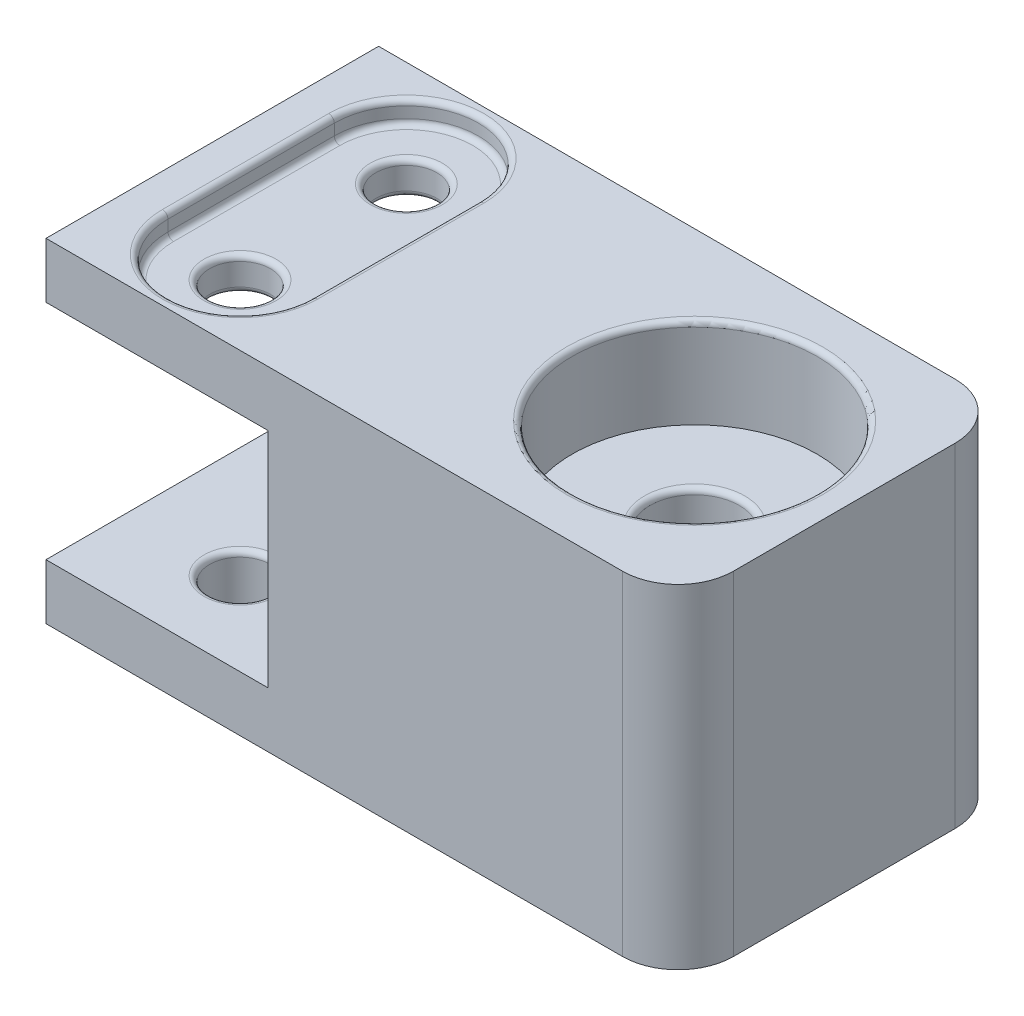
SolidWorks part; units mm, degrees
ref_plane "Front Plane" through (0, 0, 0) normal (0, 0, 1) x (1, 0, 0)
ref_plane "Top Plane" through (0, 0, 0) normal (0, 1, 0) x (1, 0, 0)
ref_plane "Right Plane" through (0, 0, 0) normal (1, 0, 0) x (0, 0, -1)
sketch "Sketch4" plane through (0, 0, 0) normal (0, 1, 0) x (1, 0, 0)
  line L1 (-28.5, -15) -> (28.5, -15)
  line L2 (-28.5, -15) -> (-28.5, 15)
  line L3 (-28.5, 15) -> (28.5, 15)
  line L4 (28.5, -15) -> (28.5, 15)
  line L5 (-28.5, -15) -> (28.5, 15) construction
  line L6 (-28.5, 15) -> (28.5, -15) construction
  point P0 (0, 0)
  dimension "D1" = 57
  dimension "D2" = 30
extrude "Boss-Extrude2" add sketch "Sketch4" along normal blind 5
sketch "Sketch5" plane through (0, 5, 0) normal (0, 1, 0) x (1, 0, 0)
  line L0 (-28.5, -15) -> (28.5, -15) construction
  line L1 (28.5, 15) -> (-8.5, 15)
  line L2 (28.5, 15) -> (28.5, -15)
  line L3 (28.5, -15) -> (-8.5, -15)
  line L4 (-8.5, 15) -> (-8.5, -15)
  line L5 (28.5, 15) -> (-8.5, -15) construction
  line L6 (28.5, -15) -> (-8.5, 15) construction
  line L7 (-28.5, 15) -> (-28.5, -15) construction
  point P4 (10, 0)
  dimension "D1" = 20
extrude "Boss-Extrude3" add sketch "Sketch5" along normal blind 20.1
sketch "Sketch6" plane through (0, 25.1, 0) normal (0, 1, 0) x (1, 0, 0)
  line L0 (28.5, -15) -> (28.5, 15) construction
  line L1 (28.5, 15) -> (-8.5, 15) construction
  line L3 (-8.5, -15) -> (28.5, -15) construction
  line L5 (-8.5, 15) -> (-28.5, 15) construction
  line L6 (-28.5, 15) -> (-28.5, -15) construction
  line L7 (-28.5, -15) -> (-8.5, -15) construction
  line L8 (28.5, -15) -> (28.5, 15)
  line L9 (28.5, 15) -> (-8.5, 15)
  line L11 (-8.5, -15) -> (28.5, -15)
  line L13 (-8.5, 15) -> (-28.5, 15)
  line L14 (-28.5, 15) -> (-28.5, -15)
  line L15 (-28.5, -15) -> (-8.5, -15)
extrude "Boss-Extrude4" add sketch "Sketch6" along normal blind 5
sketch "Sketch7" plane through (0, 30.1, 0) normal (0, 1, 0) x (1, 0, 0)
  line L0 (-28.5, -15) -> (28.5, -15) construction
  line L1 (-28.5, 15) -> (-28.5, -15) construction
  line L2 (-28.5, 0) -> (28.5, 0) construction
  line L3 (28.5, -15) -> (28.5, 15) construction
  circle A0 centre (-18.5, -7.5) radius 2.75
  circle A1 centre (-18.5, 7.5) radius 2.75
  dimension "D1" = 5.5
  dimension "D2" = 7.5
  dimension "D3" = 10
extrude "Cut-Extrude3" cut sketch "Sketch7" against normal through all
fillet "Fillet5" radius 0.5 8 edges at (-18.5, 5, -10.25) (-18.5, 0, -10.25) (-18.5, 5, 4.75) (-18.5, 0, 10.25) (-18.5, 25.1, -4.75) (-18.5, 30.1, -10.25) (-18.5, 25.1, 10.25) (-18.5, 30.1, 10.25)
sketch "Sketch8" plane through (0, 30.1, 0) normal (0, 1, 0) x (1, 0, 0)
  line L0 (-8.5, 15) -> (-8.5, -15) construction
  line L1 (-8.5, 15) -> (-8.5, -15) construction
  line L2 (28.5, -15) -> (28.5, 15) construction
  circle A1 centre (15, 0) radius 11.049
  dimension "D1" = 22.098
  dimension "D2" = 13.5
extrude "Cut-Extrude4" cut sketch "Sketch8" against normal blind 8.128 contours A1
fillet "Fillet6" radius 5 2 edges at (28.5, 15.05, -15) (28.5, 15.05, 15)
sketch "Sketch11" plane through (0, 0, 0) normal (0, -1, 0) x (1, 0, 0)
  circle A1 centre (15, 0) radius 11.049 construction
  circle A2 centre (15, 0) radius 11.049
extrude "Cut-Extrude5" cut sketch "Sketch11" against normal blind 8.128
sketch "Sketch12" plane through (0, 8.128, 0) normal (0, -1, 0) x (1, 0, 0)
  circle A0 centre (15, 0) radius 4.025
  circle A1 centre (15, 0) radius 11.049
  circle A4 centre (15, 0) radius 11.049
  dimension "D2" = 8.05
  dimension "D1" = 0
extrude "Cut-Extrude6" cut sketch "Sketch12" against normal through all contours A0
fillet "Fillet7" radius 0.5 4 edges at (15, 30.1, 11.049) (15, 8.128, -4.025) (15, 21.972, 4.025) (15, 0, -11.049)
sketch "Sketch13" plane through (0, 30.1, 0) normal (0, 1, 0) x (1, 0, 0)
  line L0 (-25, -7.5) -> (-25, 7.5)
  line L1 (-12, -7.5) -> (-12, 7.5)
  arc A0 (-25, -7.5) -> (-12, -7.5) centre (-18.5, -7.5) ccw
  arc A1 (-12, 7.5) -> (-25, 7.5) centre (-18.5, 7.5) ccw
  dimension "D1" = 13
extrude "Cut-Extrude7" cut sketch "Sketch13" against normal blind 2
fillet "Fillet8" radius 0.5 10 edges at (-12, 28.1, 0) (-18.5, 28.1, 14) (-25, 28.1, 0) (-12, 30.1, 0) (-18.5, 30.1, 14) (-25, 30.1, 0) (-18.5, 28.1, -14) (-18.5, 30.1, -14) (-18.5, 28.1, 10.25) (-18.5, 28.1, -4.75)
